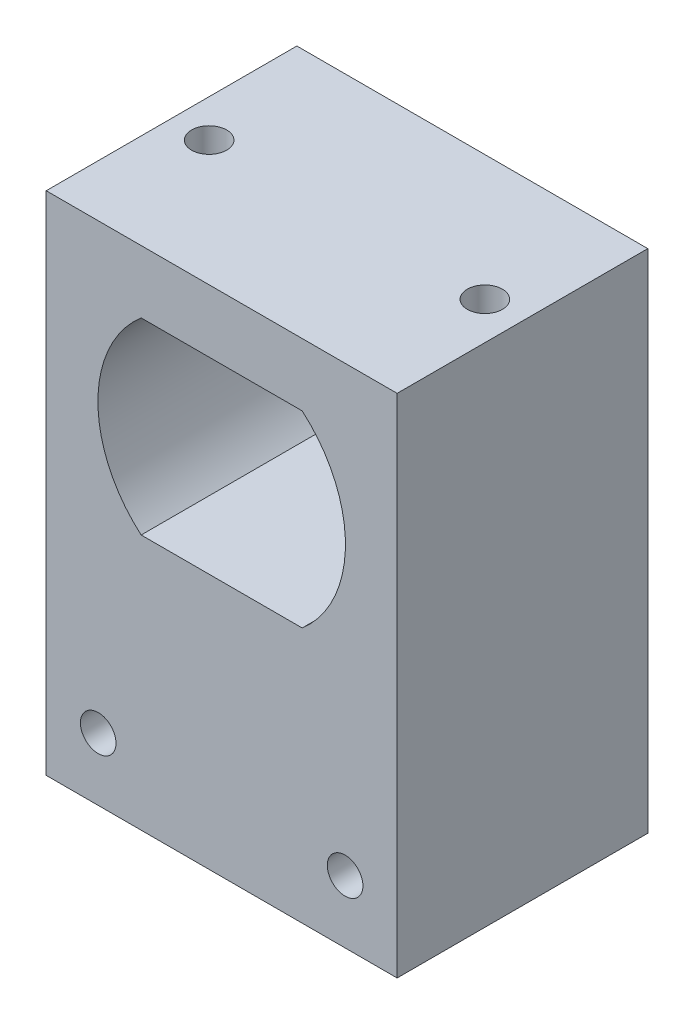
SolidWorks part; units mm, degrees
ref_plane "Front Plane" through (0, 0, 0) normal (0, 0, 1) x (1, 0, 0)
ref_plane "Top Plane" through (0, 0, 0) normal (0, 1, 0) x (1, 0, 0)
ref_plane "Right Plane" through (0, 0, 0) normal (1, 0, 0) x (0, 0, -1)
sketch "Sketch4" plane through (0, 0, 0) normal (0, 0, 1) x (1, 0, 0)
  line L1 (-14, 20.2) -> (14, 20.2)
  line L2 (-14, 20.2) -> (-14, -20.2)
  line L3 (-14, -20.2) -> (14, -20.2)
  line L4 (14, 20.2) -> (14, -20.2)
  line L5 (-14, 20.2) -> (14, -20.2) construction
  line L6 (-14, -20.2) -> (14, 20.2) construction
  point P0 (0, 0)
  dimension "D1" = 28
  dimension "D2" = 40.4
extrude "Boss-Extrude1" add sketch "Sketch4" along normal blind 20
sketch "Sketch5" plane through (0, 0, 20) normal (0, 0, 1) x (1, 0, 0)
  line L0 (14, 20.2) -> (-14, 20.2) construction
  line L3 (-6.4238, 15.2) -> (6.4238, 15.2)
  line L4 (0, 7.7) -> (0, 0) construction
  line L5 (-6.4238, 0.2) -> (6.4238, 0.2)
  line L6 (-9.875, 7.7) -> (9.875, 7.7) construction
  arc A1 (-6.4238, 15.2) -> (-6.4238, 0.2) centre (0, 7.7) ccw
  arc A2 (6.4238, 0.2) -> (6.4238, 15.2) centre (0, 7.7) ccw
  dimension "D1" = 19.75
  dimension "D2" = 15
  dimension "D3" = 5
extrude "Cut-Extrude1" cut sketch "Sketch5" against normal through all
sketch "Sketch6" plane through (0, 0, 20) normal (0, 0, 1) x (1, 0, 0)
  line L0 (0, 20.2) -> (0, -20.2) construction
  line L1 (14, 20.2) -> (-14, 20.2) construction
  line L2 (-14, -20.2) -> (14, -20.2) construction
  line L3 (-9.85, -15.2) -> (9.85, -15.2) construction
  circle A4 centre (-9.85, -15.2) radius 1.42
  circle A5 centre (9.85, -15.2) radius 1.42
  dimension "D1" = 5
  dimension "D3" = 19.7
  dimension "D2" = 2.84
extrude "Cut-Extrude3" cut sketch "Sketch6" against normal blind 10
sketch "Sketch7" plane through (0, 0, 0) normal (0, 0, 1) x (1, 0, 0)
  line L0 (-14, 20.2) -> (-14, -20.2) construction
  line L1 (12, -12.2) -> (-12, -12.2)
  line L2 (12, -12.2) -> (12, -18.2)
  line L3 (12, -18.2) -> (-12, -18.2)
  line L4 (-12, -12.2) -> (-12, -18.2)
  line L5 (12, -12.2) -> (-12, -18.2) construction
  line L6 (12, -18.2) -> (-12, -12.2) construction
  line L7 (0, -20.2) -> (0, -15.2) construction
  line L8 (-14, -20.2) -> (14, -20.2) construction
  point P0 (0, -15.2)
  dimension "D1" = 2
  dimension "D2" = 2
  dimension "D3" = 6
extrude "Cut-Extrude4" cut sketch "Sketch7" along normal blind 10
sketch "Sketch8" plane through (0, 20.2, 0) normal (0, 1, 0) x (1, 0, 0)
  line L0 (-14, -10) -> (14, -10) construction
  line L1 (-14, -20) -> (-14, 0) construction
  line L2 (14, -20) -> (14, 0) construction
  line L3 (0, 0) -> (0, -20) construction
  line L4 (14, 0) -> (-14, 0) construction
  line L5 (14, -20) -> (-14, -20) construction
  circle A0 centre (-11, -10) radius 1.4
  circle A1 centre (11, -10) radius 1.4
  dimension "D1" = 2.8
  dimension "D2" = 2.8
  dimension "D3" = 3
  dimension "D4" = 3
extrude "Cut-Extrude5" cut sketch "Sketch8" against normal blind 8
